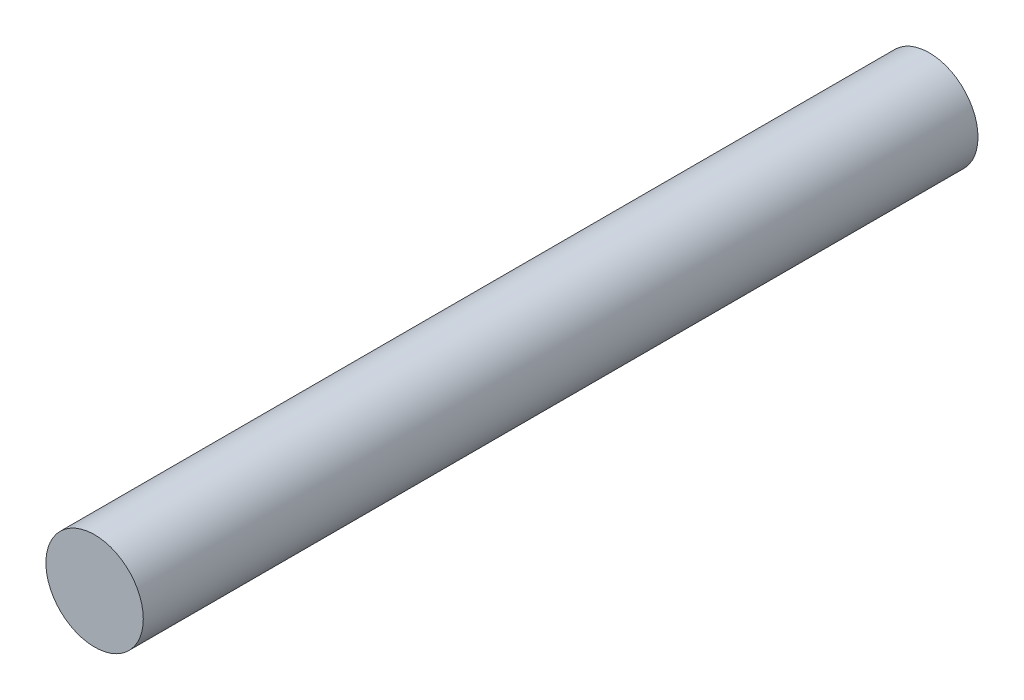
SolidWorks part; units mm, degrees
ref_plane "Front Plane" through (0, 0, 0) normal (0, 0, 1) x (1, 0, 0)
ref_plane "Top Plane" through (0, 0, 0) normal (0, 1, 0) x (1, 0, 0)
ref_plane "Right Plane" through (0, 0, 0) normal (1, 0, 0) x (0, 0, -1)
sketch "Sketch1" plane through (0, 0, 0) normal (0, 0, 1) x (1, 0, 0)
  circle A0 centre (0, 0) radius 1.75
  dimension "D1" = 3.5
extrude "Boss-Extrude1" add sketch "Sketch1" along normal blind 30
